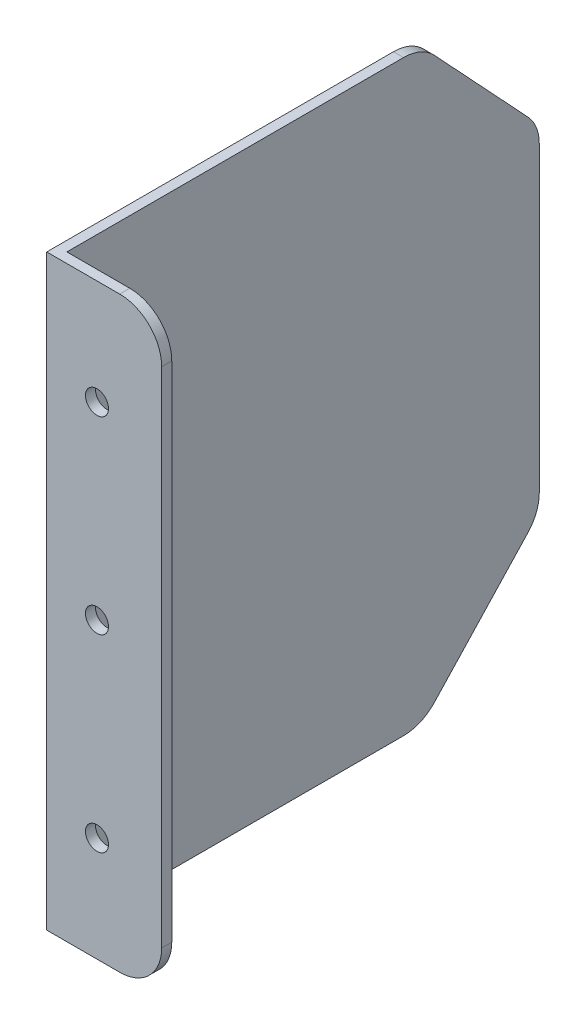
SolidWorks part; units mm, degrees
ref_plane "Front Plane" through (0, 0, 0) normal (0, 0, 1) x (1, 0, 0)
ref_plane "Top Plane" through (0, 0, 0) normal (0, 1, 0) x (1, 0, 0)
ref_plane "Right Plane" through (0, 0, 0) normal (1, 0, 0) x (0, 0, -1)
sketch "Sketch1" plane through (0, 0, 0) normal (1, 0, 0) x (0, 0, -1)
  line L1 (0, 0) -> (115, 0)
  line L2 (0, 0) -> (0, -140)
  line L3 (0, -140) -> (115, -140)
  line L4 (115, 0) -> (115, -140)
  dimension "D1" = 115
  dimension "D2" = 140
extrude "Boss-Extrude1" add sketch "Sketch1" along normal blind 2.4
sketch "Sketch2" plane through (2.4, 0, 0) normal (1, 0, 0) x (0, 0, -1)
  line L0 (87, 0) -> (115, -30)
  line L1 (115, 0) -> (0, 0) construction
  line L2 (115, -140) -> (115, 0) construction
  line L3 (115, -30) -> (142.6162, -32.5054)
  line L4 (142.6162, -32.5054) -> (142.6162, 14.8756)
  line L5 (142.6162, 14.8756) -> (87, 0)
  line L6 (115, -110) -> (87, -140)
  line L7 (0, -140) -> (115, -140) construction
  line L8 (87, -140) -> (87, -152.6611)
  line L9 (87, -152.6611) -> (136.31, -152.6611)
  line L10 (136.31, -152.6611) -> (115, -110)
  line L12 (0, 0) -> (0, -140) construction
  dimension "D1" = 30
  dimension "D2" = 87
  dimension "D3" = 87
  dimension "D4" = 30
extrude "Cut-Extrude1" cut sketch "Sketch2" against normal through all
fillet "Fillet1" radius 10 4 edges at (1.2, -140, -87) (1.2, -110, -115) (1.2, -30, -115) (1.2, 0, -87)
sketch "Sketch3" plane through (2.4, 0, 0) normal (1, 0, 0) x (0, 0, -1)
  line L0 (82.6545, 0) -> (0, 0) construction
  line L1 (0, -140) -> (2.4, -140)
  line L2 (0, -140) -> (0, 0)
  line L3 (0, 0) -> (2.4, 0)
  line L4 (2.4, -140) -> (2.4, 0)
  dimension "D1" = 2.4
extrude "Boss-Extrude2" add sketch "Sketch3" along normal blind 25
fillet "Fillet2" radius 10 2 edges at (27.4, -140, -1.2) (27.4, 0, -1.2)
sketch "Sketch4" plane through (0, 0, 0) normal (0, 0, 1) x (1, 0, 0)
  line L0 (17.4, 0) -> (0, 0) construction
  line L1 (17.4, -140) -> (0, -140) construction
  line L2 (27.4, -10) -> (27.4, -130) construction
  circle A0 centre (11.975, -70) radius 2.75
  circle A1 centre (11.975, -25) radius 2.75
  circle A2 centre (11.975, -115) radius 2.75
  point P12 (27.4, -70)
  dimension "D1" = 5.5
  dimension "D2" = 5.5
  dimension "D3" = 5.5
  dimension "D4" = 25
  dimension "D5" = 25
extrude "Cut-Extrude2" cut sketch "Sketch4" against normal through all
